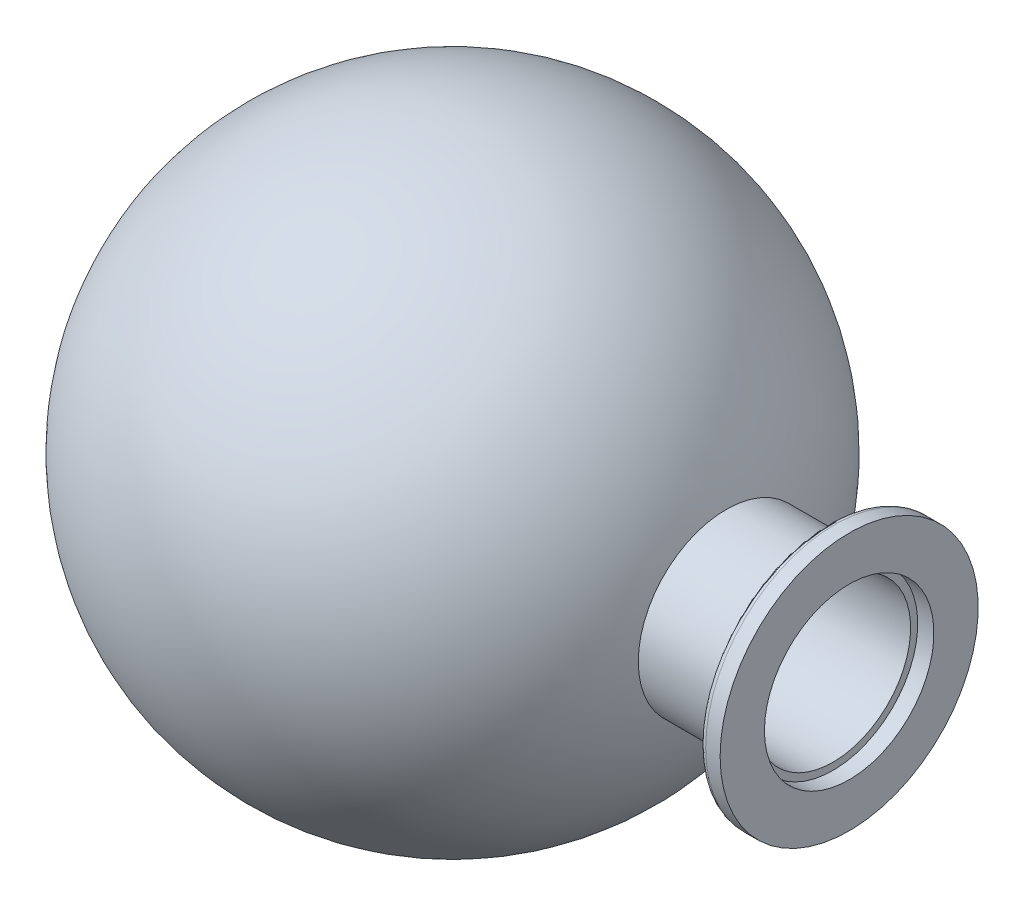
SolidWorks part; units mm, degrees
ref_plane "Plan de face" through (0, 0, 0) normal (0, 0, 1) x (1, 0, 0)
ref_plane "Plan de dessus" through (0, 0, 0) normal (0, 1, 0) x (1, 0, 0)
ref_plane "Plan de droite" through (0, 0, 0) normal (1, 0, 0) x (0, 0, -1)
sketch "Esquisse1" plane through (0, 0, 0) normal (0, 0, 1) x (1, 0, 0)
  line L0 (-48.091, 0) -> (51.8836, 0) construction
  line L1 (-42.7996, 12) -> (58.8183, 12)
  line L2 (0, -6.5913) -> (0, 53.9928) construction
  line L3 (61.3183, 19.95) -> (61.3183, 13.1)
  line L4 (61.3183, 19.95) -> (59.0857, 19.95)
  line L5 (42.3183, 13.6) -> (56.6169, 13.6)
  line L6 (56.6169, 13.6) -> (58.1197, 19.2088)
  line L8 (61.3183, 13.1) -> (58.8183, 13.1)
  line L9 (58.8183, 13.1) -> (58.8183, 12)
  arc A0 (42.3183, 13.6) -> (-42.7996, 12) centre (0, 0) ccw
  arc A2 (59.0857, 19.95) -> (58.1197, 19.2088) centre (59.0857, 18.95) ccw
  point P16 (58.3183, 19.95)
  dimension "D1" = 44.45
  dimension "D5" = 3
  dimension "D9" = 1
  dimension "D2" = 12
  dimension "D3" = 19.95
  dimension "D4" = 15
  dimension "D6" = 13.6
  dimension "D7" = 13.1
  dimension "D8" = 2.5
  dimension "D10" = 19
  dimension "D11" = 104.1179
revolve "Révolution1" add sketch "Esquisse1" angle 360 about L0
